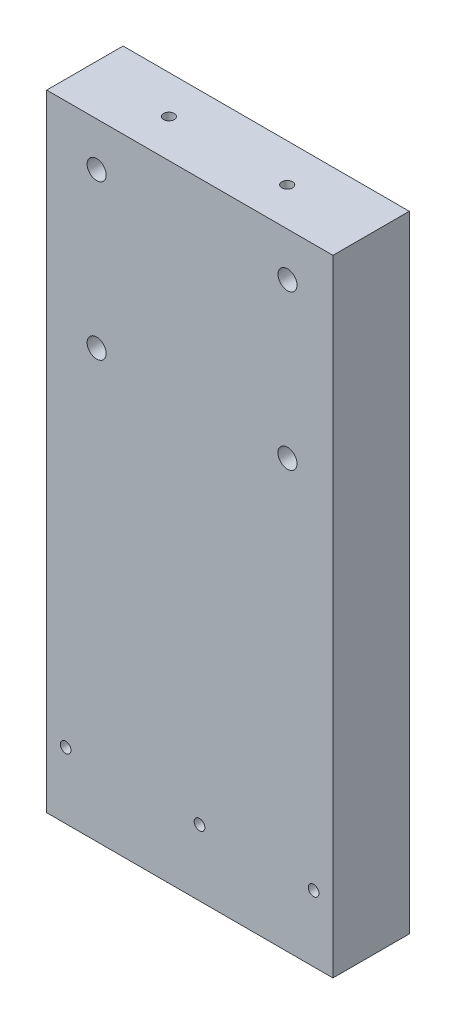
SolidWorks part; units mm, degrees
ref_plane "Front Plane" through (0, 0, 0) normal (0, 0, 1) x (1, 0, 0)
ref_plane "Top Plane" through (0, 0, 0) normal (0, 1, 0) x (1, 0, 0)
ref_plane "Right Plane" through (0, 0, 0) normal (1, 0, 0) x (0, 0, -1)
sketch "Sketch1" plane through (0, 0, 0) normal (0, 0, 1) x (1, 0, 0)
  line L0 (37.5, -82) -> (37.5, 82)
  line L1 (37.5, 82) -> (-37.5, 82)
  line L2 (-37.5, 82) -> (-37.5, -82)
  line L3 (-37.5, -82) -> (37.5, -82)
  circle A0 centre (-32.5324, -64.6627) radius 1.4
  circle A1 centre (32.4367, -64.6627) radius 1.4
  circle A2 centre (2.542, -64.6627) radius 1.4
  circle A3 centre (25.5838, 30) radius 2.5
  circle A4 centre (-24.4162, 70.5) radius 2.5
  circle A5 centre (25.5838, 70.5) radius 2.5
  circle A6 centre (-24.4162, 30) radius 2.5
extrude "Boss-Extrude1" add sketch "Sketch1" along normal blind 20
sketch "Sketch2" plane through (0, 82, 0) normal (0, 1, 0) x (1, 0, 0)
  line L0 (-37.5, -10) -> (37.5, -10)
  line L1 (-37.5, -20) -> (-37.5, 0) construction
  line L2 (37.5, -20) -> (37.5, 0) construction
  line L3 (37.5099, -19.995) -> (37.5099, 0.005)
  line L4 (37.5099, 0.005) -> (-37.4901, 0.005)
  line L5 (-37.4901, 0.005) -> (-37.4901, -19.995)
  line L6 (-37.4901, -19.995) -> (37.5099, -19.995)
  circle A0 centre (15.5099, -9.995) radius 1.4
  circle A1 centre (-15.4901, -9.995) radius 1.4
extrude "Cut-Extrude1" cut sketch "Sketch2" against normal through all contours L0 A1 | L0 A1 | L0 A0 | L0 A0 | L3 L4 L5 L6
